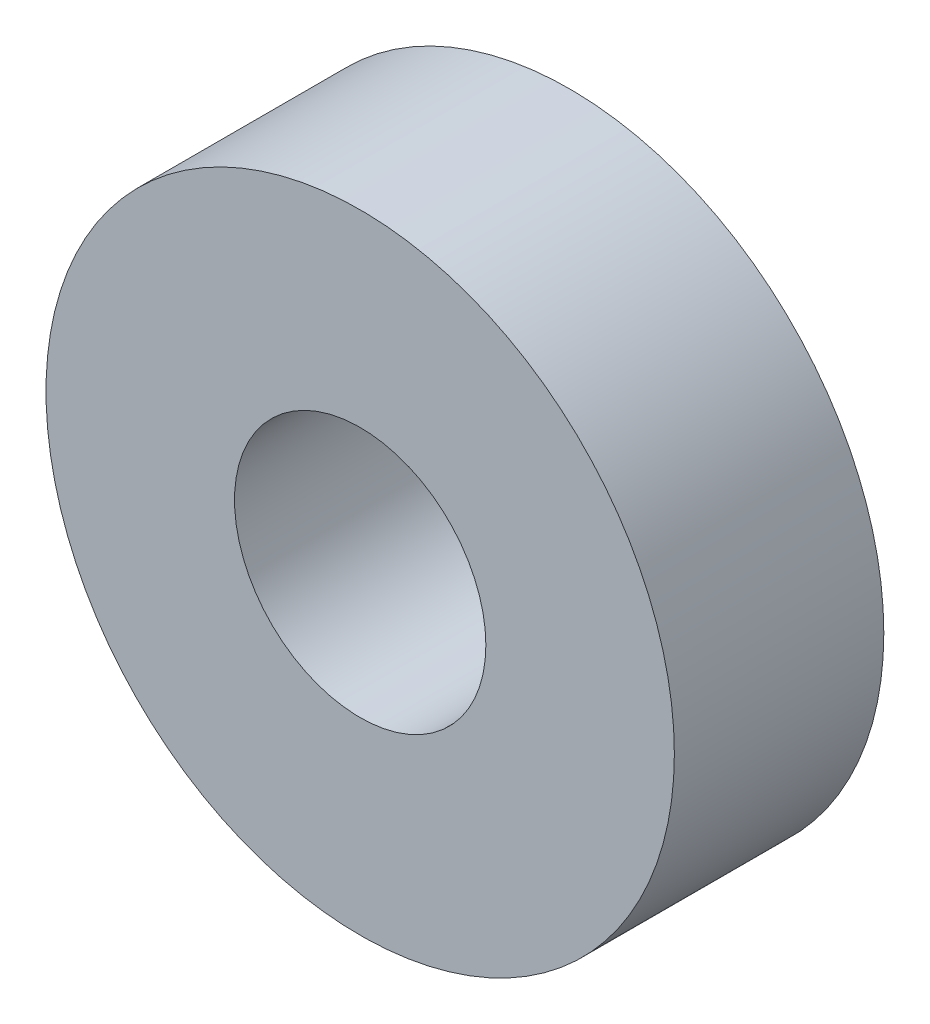
SolidWorks part; units mm, degrees
ref_plane "Front Plane" through (0, 0, 0) normal (0, 0, 1) x (1, 0, 0)
ref_plane "Top Plane" through (0, 0, 0) normal (0, 1, 0) x (1, 0, 0)
ref_plane "Right Plane" through (0, 0, 0) normal (1, 0, 0) x (0, 0, -1)
sketch "Sketch1" plane through (0, 0, 0) normal (0, 0, 1) x (1, 0, 0)
  circle A0 centre (0, 0) radius 3
  circle A1 centre (0, 0) radius 7.5
  dimension "D1" = 15
  dimension "D2" = 6
extrude "Boss-Extrude1" add sketch "Sketch1" along normal blind 5
